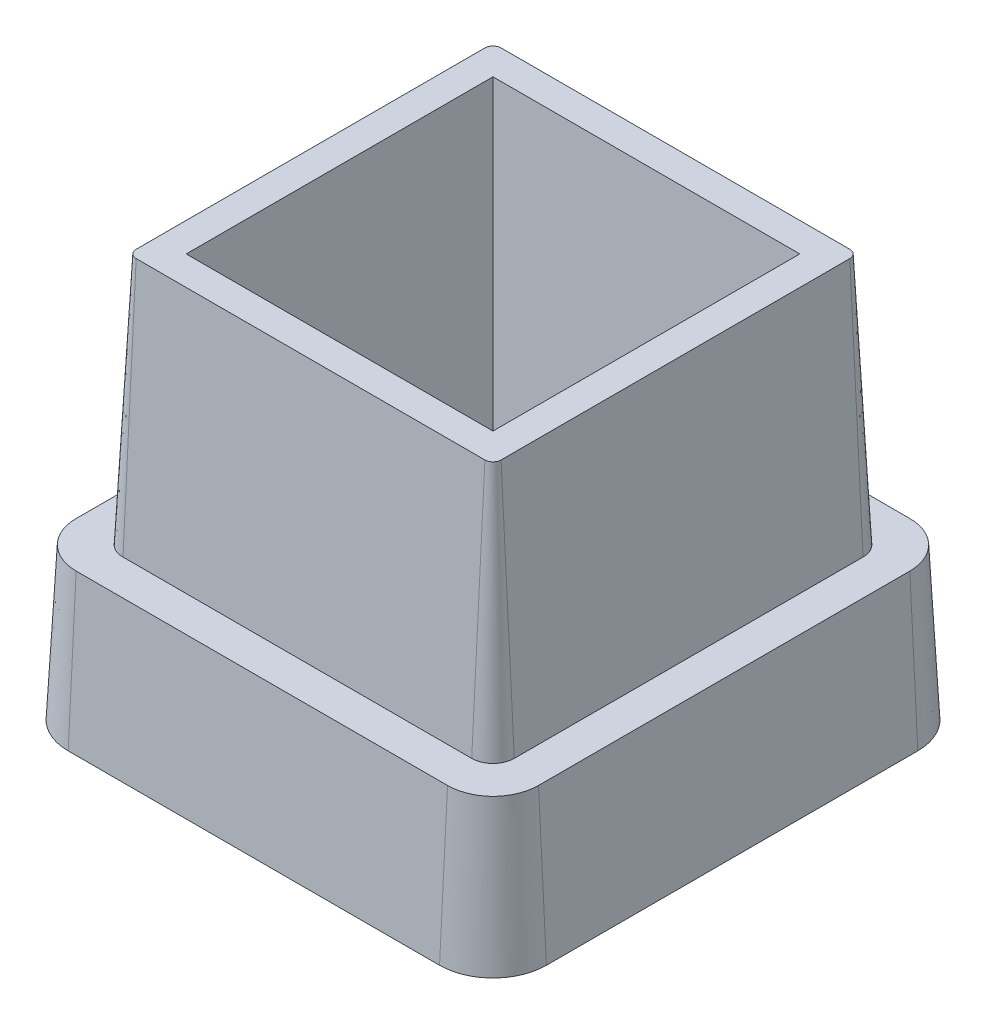
SolidWorks part; units mm, degrees
ref_plane "Front Plane" through (0, 0, 0) normal (0, 0, 1) x (1, 0, 0)
ref_plane "Top Plane" through (0, 0, 0) normal (0, 1, 0) x (1, 0, 0)
ref_plane "Right Plane" through (0, 0, 0) normal (1, 0, 0) x (0, 0, -1)
sketch "Sketch1" plane through (0, 0, 0) normal (0, 1, 0) x (1, 0, 0)
  line L0 (0, 0) -> (0, 27733.189) construction
  line L1 (0, 0) -> (-27733.189, 0) construction
  line L3 (13.5, -13.5) -> (-13.5, -13.5)
  line L4 (13.5, -13.5) -> (13.5, 13.5)
  line L5 (13.5, 13.5) -> (-13.5, 13.5)
  line L6 (-13.5, -13.5) -> (-13.5, 13.5)
  line L7 (13.5, -13.5) -> (-13.5, 13.5) construction
  line L8 (13.5, 13.5) -> (-13.5, -13.5) construction
  point P5 (0, 0)
  dimension "D1" = 27
  dimension "D2" = 27
extrude "Boss-Extrude1" add sketch "Sketch1" along normal blind 25
sketch "Sketch2" plane through (0, 25, 0) normal (0, 1, 0) x (1, 0, 0)
  line L13 (13.5, -13.5) -> (-13.5, -13.5)
  line L14 (13.5, -13.5) -> (13.5, 13.5)
  line L15 (13.5, 13.5) -> (-13.5, 13.5)
  line L16 (11.3, -11.3) -> (11.3, 11.3)
  line L17 (-11.3, -11.3) -> (11.3, -11.3)
  line L18 (-11.3, 11.3) -> (-11.3, -11.3)
  line L19 (11.3, 11.3) -> (-11.3, 11.3)
  line L20 (11.3, -11.3) -> (11.3, 11.3)
  line L21 (-11.3, -11.3) -> (11.3, -11.3)
  line L22 (-11.3, 11.3) -> (-11.3, -11.3)
  line L23 (11.3, 11.3) -> (-11.3, 11.3)
  line L24 (-13.5, -13.5) -> (-13.5, 13.5)
  line L25 (13.5, -13.5) -> (-13.5, 13.5) construction
  line L26 (13.5, 13.5) -> (-13.5, -13.5) construction
  point P0 (0, 0)
  dimension "D1" = 2.2
extrude "Cut-Extrude1" cut sketch "Sketch2" against normal blind 15.6
sketch "Sketch3" plane through (0, 25, 0) normal (0, 1, 0) x (1, 0, 0)
  line L1 (9.5, -9.5) -> (-9.5, -9.5)
  line L2 (9.5, -9.5) -> (9.5, 9.5)
  line L3 (9.5, 9.5) -> (-9.5, 9.5)
  line L4 (-9.5, -9.5) -> (-9.5, 9.5)
  line L5 (9.5, -9.5) -> (-9.5, 9.5) construction
  line L6 (9.5, 9.5) -> (-9.5, -9.5) construction
  point P0 (0, 0)
  dimension "D1" = 19
  dimension "D2" = 19
extrude "Cut-Extrude2" cut sketch "Sketch3" against normal blind 22.8
fillet "Fillet1" radius 0.5 4 edges at (-11.3, 17.2, 11.3) (-11.3, 17.2, -11.3) (11.3, 17.2, 11.3) (11.3, 17.2, -11.3)
fillet "Fillet2" radius 2 4 edges at (-13.5, 4.7, 13.5) (13.5, 4.7, 13.5) (13.5, 4.7, -13.5) (-13.5, 4.7, -13.5)
draft "Draft12" type of draft neutral plane draft angle 3 faces to draft 20 face at (13.5, 4.7, 0) face at (9.5, 13.6, 0) face at (0, 13.6, 9.5) face at (-9.5, 13.6, 0) face at (0, 13.6, -9.5) face at (-11.1018, 17.2, -11.1018) face at (-12.7071, 4.7, -12.7071) face at (-13.5, 4.7, 0) face at (-11.3, 17.2, 0) face at (-11.1018, 17.2, 11.1018) face at (-12.7071, 4.7, 12.7071) face at (0, 4.7, 13.5) face at (12.7071, 4.7, 12.7071) face at (11.1018, 17.2, 11.1018) face at (0, 17.2, 11.3) face at (11.3, 17.2, 0) face at (11.1018, 17.2, -11.1018) face at (0, 17.2, -11.3) face at (0, 4.7, -13.5) face at (12.7071, 4.7, -12.7071) neutral plane through (0, 25, 0) neutral plane normal (0, 1, 0) parameters "D1"=3
